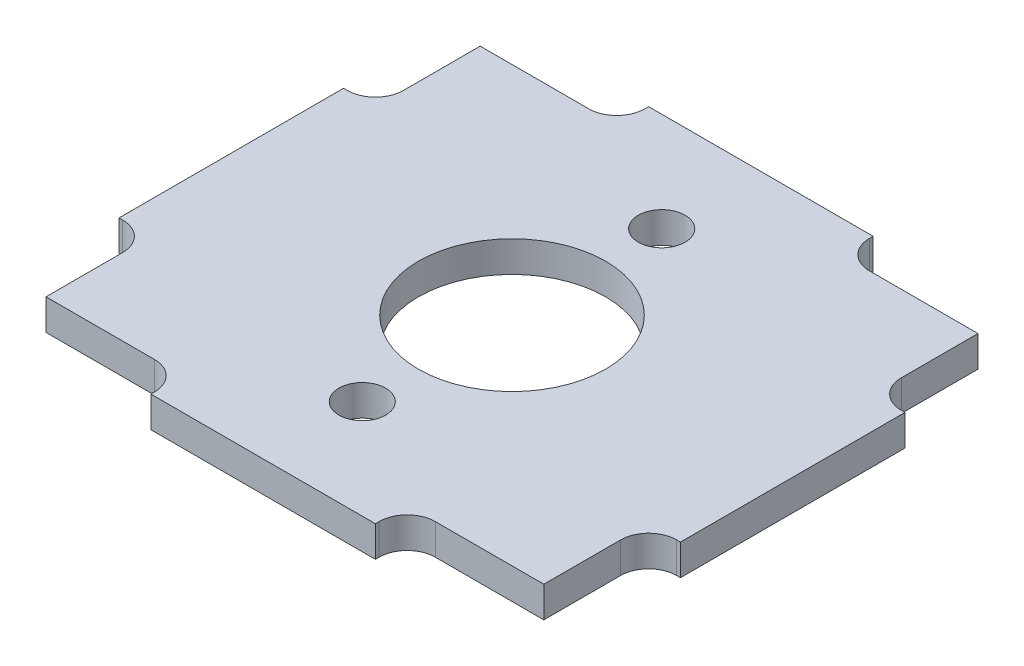
SolidWorks part; units mm, degrees
material "PVC hart"
ref_plane "Ebene vorne" through (0, 0, 0) normal (0, 0, 1) x (1, 0, 0)
ref_plane "Ebene oben" through (0, 0, 0) normal (0, 1, 0) x (1, 0, 0)
ref_plane "Ebene rechts" through (0, 0, 0) normal (1, 0, 0) x (0, 0, -1)
sketch "Skizze1" plane through (0, 0, 0) normal (0, 1, 0) x (1, 0, 0)
  line L0 (-13.3, -6) -> (-13.3, -11.6)
  line L1 (-6, 11.6) -> (-6, 13.3)
  line L2 (-6, 13.3) -> (6, 13.3)
  line L3 (6, 13.3) -> (6, 11.6)
  line L4 (13.3, 6) -> (15, 6)
  line L5 (15, 6) -> (15, -6)
  line L6 (15, -6) -> (13.3, -6)
  line L7 (-6, -13.3) -> (-6, -11.6)
  line L8 (0, 13.3) -> (0, -13.3) construction
  line L9 (13.3, -6) -> (13.3, -11.6)
  line L10 (-6, -11.6) -> (-13.3, -11.6)
  line L11 (-15, -6) -> (-13.3, -6)
  line L12 (13.3, 11.6) -> (13.3, 6)
  line L13 (0, 8) -> (0, -8) construction
  line L14 (-15, 0) -> (15, 0) construction
  line L15 (6, 11.6) -> (13.3, 11.6)
  line L16 (-15, 6) -> (-15, -6)
  line L17 (-13.3, 6) -> (-15, 6)
  line L18 (6, -11.6) -> (13.3, -11.6)
  line L19 (-13.3, 11.6) -> (-13.3, 6)
  line L20 (-6, 11.6) -> (-13.3, 11.6)
  line L24 (6, -13.3) -> (6, -11.6)
  line L25 (-6, -13.3) -> (6, -13.3)
  line L26 (-6, -11.6) -> (-6, -13.3)
  circle A0 centre (0, -8) radius 1.25
  circle A1 centre (0, 8) radius 1.25
  circle A2 centre (0, 0) radius 5
  point P20 (0, 0)
  dimension "D7" = 2.5
  dimension "D8" = 1.7
  dimension "D9" = 26.6
  dimension "D3" = 16
  dimension "D1" = 10
  dimension "D2" = 12
  dimension "D4" = 30
extrude "Aufsatz-Linear austragen1" add sketch "Skizze1" against normal mid plane 1.65
fillet "Verrundung1" radius 1.5 8 edges at (6, 0, -11.6) (6, 0, 11.6) (13.3, 0, -6) (13.3, 0, 6) (-6, 0, 11.6) (-13.3, 0, 6) (-13.3, 0, -6) (-6, 0, -11.6)
